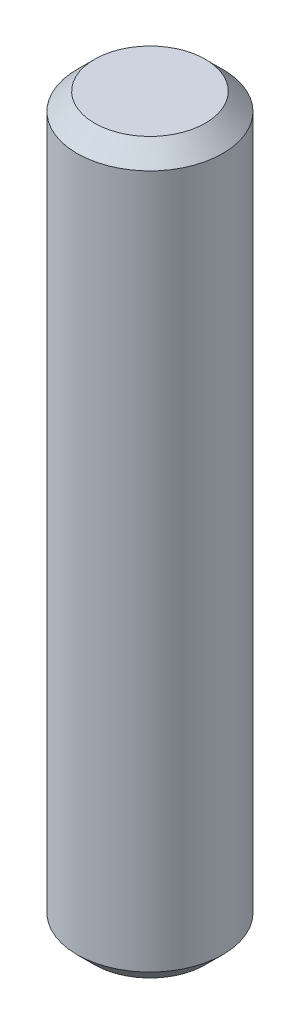
SolidWorks part; units mm, degrees
ref_plane "Front Plane" through (0, 0, 0) normal (0, 0, 1) x (1, 0, 0)
ref_plane "Top Plane" through (0, 0, 0) normal (0, 1, 0) x (1, 0, 0)
ref_plane "Right Plane" through (0, 0, 0) normal (1, 0, 0) x (0, 0, -1)
sketch "Sketch1" plane through (0, 0, 0) normal (0, 1, 0) x (1, 0, 0)
  circle A0 centre (0, 0) radius 6.35
  dimension "D1" = 12.7
extrude "Boss-Extrude1" add sketch "Sketch1" along normal mid plane 63.5
chamfer "Chamfer1" distance 1.524 angle 45 2 edges at (0, -31.75, 6.35) (0, 31.75, 6.35)
